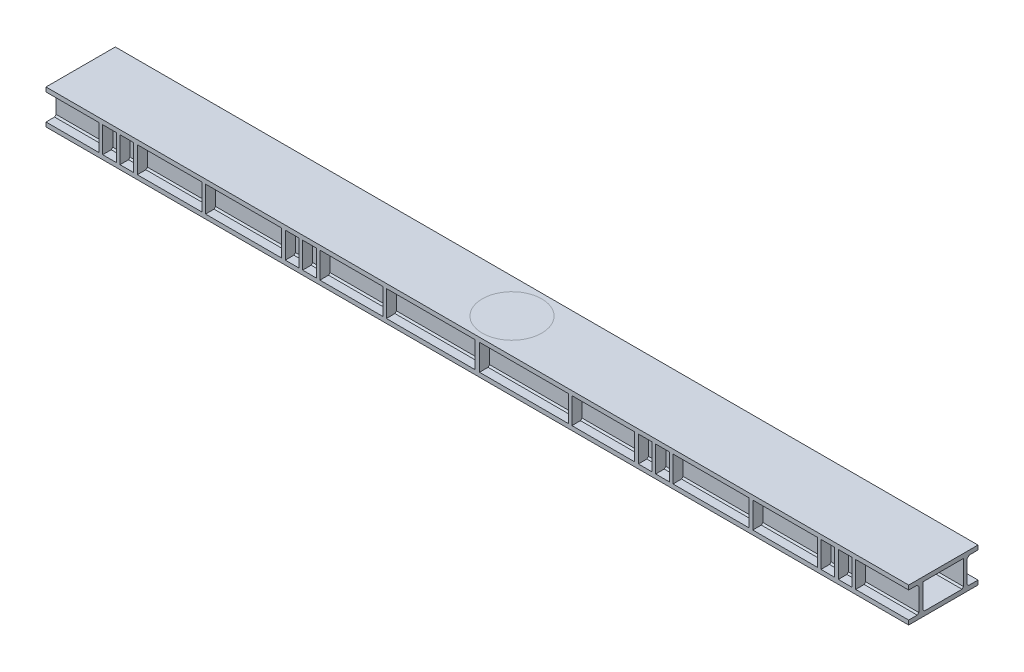
SolidWorks part; units mm, degrees
ref_plane "Front Plane" through (0, 0, 0) normal (0, 0, 1) x (1, 0, 0)
ref_plane "Top Plane" through (0, 0, 0) normal (0, 1, 0) x (1, 0, 0)
ref_plane "Right Plane" through (0, 0, 0) normal (1, 0, 0) x (0, 0, -1)
sketch "Sketch3" plane through (0, 0, 0) normal (0, 0, 1) x (1, 0, 0)
  line L0 (4163.3024, -161.9761) -> (-1811.6976, -161.9761)
  line L1 (-1811.6976, -161.9761) -> (-1811.6976, -131.9761)
  line L4 (4163.3024, 48.0239) -> (-1811.6976, 48.0239)
  line L5 (-1811.6976, 48.0239) -> (-1811.6976, 78.0239)
  line L6 (-1811.6976, 78.0239) -> (4163.3024, 78.0239)
  line L8 (545.802, 48.0239) -> (545.802, -131.9761)
  line L10 (545.802, -131.9761) -> (520.802, -131.9761)
  line L11 (1190.8024, 48.0239) -> (1160.8024, 48.0239)
  line L13 (4163.3024, -131.9761) -> (-1811.6976, -131.9761)
  line L16 (520.802, -131.9761) -> (520.802, 48.0239)
  line L17 (85.6596, 48.0239) -> (60.6596, 48.0239)
  line L18 (60.6596, 48.0239) -> (60.6596, -131.9761)
  line L19 (60.6596, -131.9761) -> (85.6596, -131.9761)
  line L20 (85.6596, -131.9761) -> (85.6596, 48.0239)
  line L21 (-34.3404, 48.0239) -> (-34.3404, -131.9761)
  line L26 (-34.3404, -131.9761) -> (-59.3404, -131.9761)
  line L35 (-59.3404, -131.9761) -> (-59.3404, 48.0239)
  line L36 (-59.3404, 48.0239) -> (-34.3404, 48.0239)
  line L37 (-154.3404, 48.0239) -> (-154.3404, -131.9761)
  line L38 (-154.3404, -131.9761) -> (-179.3404, -131.9761)
  line L39 (-179.3404, -131.9761) -> (-179.3404, 48.0239)
  line L40 (-179.3404, 48.0239) -> (-154.3404, 48.0239)
  line L41 (-1179.1976, 48.0239) -> (-1179.1976, -131.9761)
  line L42 (-1179.1976, -131.9761) -> (-1204.1976, -131.9761)
  line L43 (-1204.1976, -131.9761) -> (-1204.1976, 48.0239)
  line L44 (-1204.1976, 48.0239) -> (-1179.1976, 48.0239)
  line L45 (-1299.1976, 48.0239) -> (-1299.1976, -131.9761)
  line L46 (-1299.1976, -131.9761) -> (-1324.1976, -131.9761)
  line L47 (-1324.1976, -131.9761) -> (-1324.1976, 48.0239)
  line L48 (-1324.1976, 48.0239) -> (-1299.1976, 48.0239)
  line L49 (-1419.1976, 48.0239) -> (-1419.1976, -131.9761)
  line L50 (-1419.1976, -131.9761) -> (-1444.1976, -131.9761)
  line L51 (-1444.1976, -131.9761) -> (-1444.1976, 48.0239)
  line L52 (-1444.1976, 48.0239) -> (-1419.1976, 48.0239)
  line L53 (520.802, 48.0239) -> (545.802, 48.0239)
  line L54 (-706.6976, -131.9761) -> (-706.6976, 48.0239)
  line L55 (-706.6976, 48.0239) -> (-731.6976, 48.0239)
  line L56 (-731.6976, 48.0239) -> (-731.6976, -131.9761)
  line L57 (-731.6976, -131.9761) -> (-706.6976, -131.9761)
  line L58 (1175.8024, 344.1246) -> (1175.8024, -1702.9744) construction
  line L59 (3083.3024, -131.9761) -> (3058.3024, -131.9761)
  line L60 (3083.3024, 48.0239) -> (3083.3024, -131.9761)
  line L61 (3058.3024, 48.0239) -> (3083.3024, 48.0239)
  line L62 (3058.3024, -131.9761) -> (3058.3024, 48.0239)
  line L63 (1830.8027, 48.0239) -> (1805.8027, 48.0239)
  line L64 (3795.8024, 48.0239) -> (3770.8024, 48.0239)
  line L65 (3795.8024, -131.9761) -> (3795.8024, 48.0239)
  line L66 (3770.8024, -131.9761) -> (3795.8024, -131.9761)
  line L67 (3770.8024, 48.0239) -> (3770.8024, -131.9761)
  line L68 (3675.8024, 48.0239) -> (3650.8024, 48.0239)
  line L69 (3675.8024, -131.9761) -> (3675.8024, 48.0239)
  line L70 (3650.8024, -131.9761) -> (3675.8024, -131.9761)
  line L71 (3650.8024, 48.0239) -> (3650.8024, -131.9761)
  line L72 (3555.8024, 48.0239) -> (3530.8024, 48.0239)
  line L73 (3555.8024, -131.9761) -> (3555.8024, 48.0239)
  line L74 (3530.8024, -131.9761) -> (3555.8024, -131.9761)
  line L75 (3530.8024, 48.0239) -> (3530.8024, -131.9761)
  line L76 (2530.9451, 48.0239) -> (2505.9451, 48.0239)
  line L77 (2530.9451, -131.9761) -> (2530.9451, 48.0239)
  line L78 (2505.9451, -131.9761) -> (2530.9451, -131.9761)
  line L79 (2505.9451, 48.0239) -> (2505.9451, -131.9761)
  line L80 (2410.9451, 48.0239) -> (2385.9451, 48.0239)
  line L81 (2410.9451, -131.9761) -> (2410.9451, 48.0239)
  line L82 (2385.9451, -131.9761) -> (2410.9451, -131.9761)
  line L83 (2385.9451, 48.0239) -> (2385.9451, -131.9761)
  line L84 (2265.9451, -131.9761) -> (2265.9451, 48.0239)
  line L85 (2290.9451, -131.9761) -> (2265.9451, -131.9761)
  line L86 (2290.9451, 48.0239) -> (2290.9451, -131.9761)
  line L87 (2265.9451, 48.0239) -> (2290.9451, 48.0239)
  line L88 (1830.8027, -131.9761) -> (1830.8027, 48.0239)
  line L89 (1160.8024, 48.0239) -> (1160.8024, -131.9761)
  line L90 (1805.8027, -131.9761) -> (1830.8027, -131.9761)
  line L91 (1805.8027, 48.0239) -> (1805.8027, -131.9761)
  line L92 (4163.3024, 48.0239) -> (4163.3024, 78.0239)
  line L93 (4163.3024, -161.9761) -> (4163.3024, -131.9761)
  line L94 (1160.8024, -131.9761) -> (1190.8024, -131.9761)
  line L95 (1190.8024, -131.9761) -> (1190.8024, 48.0239)
  dimension "D2" = 15
  dimension "D3" = 25
  dimension "D4" = 25
  dimension "D5" = 25
  dimension "D6" = 15
  dimension "D7" = 180
  dimension "D8" = 30
  dimension "D9" = 120
  dimension "D10" = 120
  dimension "D11" = 30
  dimension "D13" = 120
  dimension "D14" = 120
extrude "Boss-Extrude1" add sketch "Sketch3" along normal blind 480 contours L13 L58 L0 L93 | L4 L58 L13 L95 | L16 L10 L8 L4 | L13 L20 L4 L18 | L39 L13 L37 L4 | L47 L13 L45 L4 | L43 L13 L41 L4 | L4 L56 L13 L54 | L84 L87 L86 L85 | L81 L80 L83 L82 | L79 L78 L77 L76 | L65 L64 L67 L66 | L69 L68 L71 L70 | L73 L72 L75 L74 | L62 L61 L60 L59 | L88 L63 L91 L90 | L21 L26 L35 L36 | L51 L52 L49 L50
sketch "Sketch4" plane through (-1811.6976, 0, 0) normal (-1, 0, 0) x (0, 0, 1)
  line L0 (60.1205, 48.0239) -> (75, 34.6598)
  line L1 (75, 48.0239) -> (75, -131.9761)
  line L2 (480, 48.0239) -> (0, 48.0239) construction
  line L3 (480, -131.9761) -> (0, -131.9761) construction
  line L4 (75, -131.9761) -> (100, -131.9761)
  line L5 (480, -131.9761) -> (0, -131.9761) construction
  line L6 (100, -131.9761) -> (100, 48.0239)
  line L7 (480, 48.0239) -> (0, 48.0239) construction
  line L8 (100, 48.0239) -> (75, 48.0239)
  line L13 (75, 34.6598) -> (75, 48.0239)
  line L14 (75, -131.9761) -> (64.3934, -131.9761)
  line L15 (64.3934, -131.9761) -> (75, -121.3695)
  line L16 (100, -121.3695) -> (110.6066, -131.9761)
  line L17 (110.6066, -131.9761) -> (100, -131.9761)
  line L18 (380, 48.0239) -> (410, 48.0239)
  line L20 (410, 48.0239) -> (410, -131.9761)
  line L21 (410, -131.9761) -> (380, -131.9761)
  line L22 (380, -131.9761) -> (380, 48.0239)
  line L26 (424.1719, 48.0239) -> (410, 33.8521)
  line L27 (424.1719, 48.0239) -> (410, 48.0239)
  line L28 (380, -121.321) -> (369.4421, -131.9761)
  line L29 (369.4421, -131.9761) -> (380, -131.9761)
  line L30 (410, -121.5677) -> (420.8012, -131.9761)
  line L31 (420.8012, -131.9761) -> (410, -131.9761)
  line L32 (480, -161.9761) -> (480, -131.9761) construction
  line L33 (410, 33.8521) -> (410, 48.0239)
  line M2 (0, 48.0239) -> (480, 48.0239)
  dimension "D1" = 25
  dimension "D2" = 30
  dimension "D3" = 100
  dimension "D4" = 100
  dimension "D5" = 15
  dimension "D6" = 20
  dimension "D7" = 20.0421
  dimension "D8" = 15
  dimension "D9" = 15
  dimension "D10" = 15
extrude "Boss-Extrude3" add sketch "Sketch4" against normal up to surface (5975 mm away) contours L1 L0 M2 | L4 L6 L1 M2 | L15 L14 L1 | L17 L16 L6 | L31 L30 L20 | L28 L29 L22 | L22 L21 L20 M2 | L26 L20 M2 up to face at (4163.3024, 63.0239, 240)
sketch "Sketch6" plane through (0, 78.0239, 0) normal (0, 1, 0) x (1, 0, 0)
  circle A0 centre (1175.8024, -240) radius 206.0569
split line "Split Line1"
